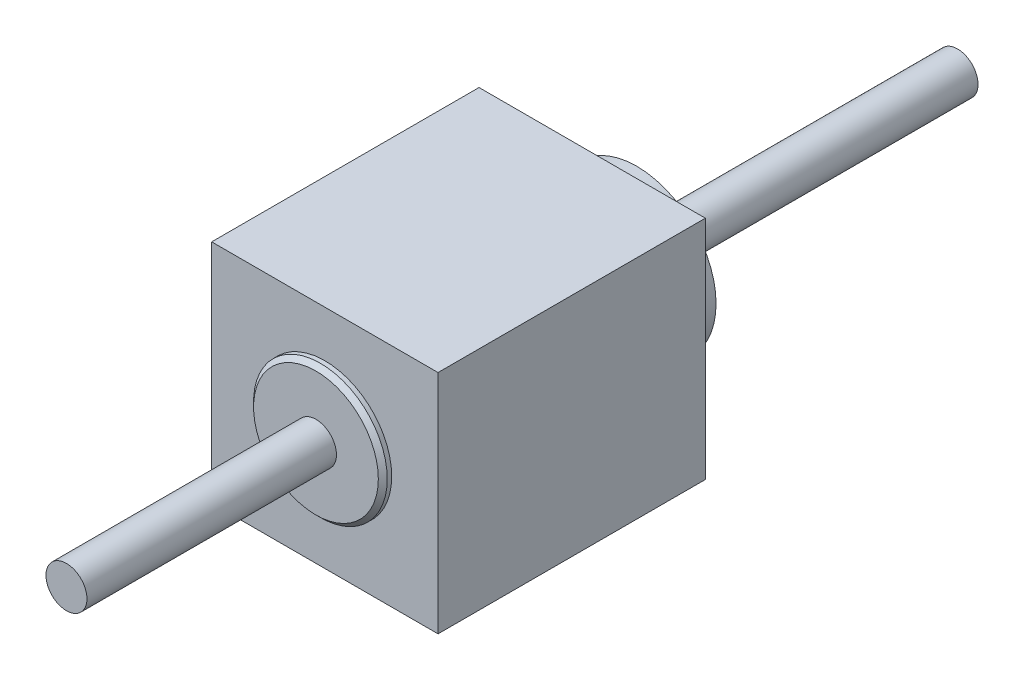
SolidWorks part; units mm, degrees
ref_plane "Front Plane" through (0, 0, 0) normal (0, 0, 1) x (1, 0, 0)
ref_plane "Top Plane" through (0, 0, 0) normal (0, 1, 0) x (1, 0, 0)
ref_plane "Right Plane" through (0, 0, 0) normal (1, 0, 0) x (0, 0, -1)
sketch "Sketch1" plane through (0, 0, 0) normal (0, 0, 1) x (1, 0, 0)
  line L1 (1.27, -1.27) -> (-1.27, -1.27)
  line L2 (1.27, -1.27) -> (1.27, 1.27)
  line L3 (1.27, 1.27) -> (-1.27, 1.27)
  line L4 (-1.27, -1.27) -> (-1.27, 1.27)
  line L5 (1.27, -1.27) -> (-1.27, 1.27) construction
  line L6 (1.27, 1.27) -> (-1.27, -1.27) construction
  point P0 (0, 0)
  dimension "D1" = 2.54
extrude "Boss-Extrude1" add sketch "Sketch1" along normal blind 3
sketch "Sketch2" plane through (0, 0, 0) normal (0, 0, -1) x (-1, 0, 0)
  circle A0 centre (0, 0) radius 0.23
  dimension "D1" = 0.46
extrude "Boss-Extrude2" add sketch "Sketch2" along normal blind 4.1
sketch "Sketch3" plane through (0, 0, 0) normal (0, 0, -1) x (-1, 0, 0)
  circle A0 centre (0, 0) radius 0.89
  dimension "D1" = 1.78
extrude "Boss-Extrude3" add sketch "Sketch3" along normal blind 0.5
sketch "Sketch4" plane through (0, 0, 3) normal (0, 0, 1) x (1, 0, 0)
  circle A0 centre (0, 0) radius 0.23
  dimension "D1" = 0.46
extrude "Boss-Extrude4" add sketch "Sketch4" along normal blind 2.9
sketch "Sketch5" plane through (0, 0, 3) normal (0, 0, 1) x (1, 0, 0)
  circle A0 centre (0, 0) radius 0.75
  dimension "D1" = 1.5
extrude "Boss-Extrude5" add sketch "Sketch5" along normal blind 0.1
chamfer "Chamfer1" distance 0.05 angle 45 1 edges at (0.75, 0, 3.1)
